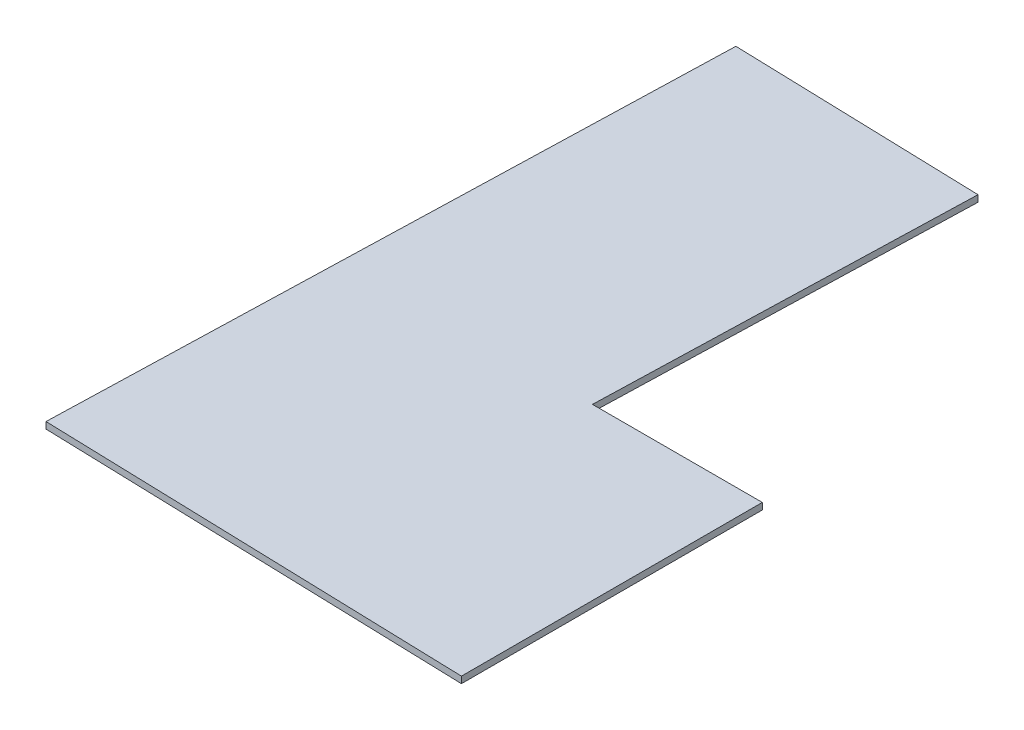
SolidWorks part; units mm, degrees
ref_plane "Front Plane" through (0, 0, 0) normal (0, 0, 1) x (1, 0, 0)
ref_plane "Top Plane" through (0, 0, 0) normal (0, 1, 0) x (1, 0, 0)
ref_plane "Right Plane" through (0, 0, 0) normal (1, 0, 0) x (0, 0, -1)
sketch "Sketch1" plane through (0, 0, 0) normal (0, 1, 0) x (1, 0, 0)
  line L1 (-241.1129, -200.9269) -> (-159.0136, -200.9269)
  line L6 (-159.0136, -200.9269) -> (-159.0136, -346.3773)
  line L7 (-159.0136, -346.3773) -> (-366.0236, -340.2039)
  line L8 (-366.0236, -340.2039) -> (-356.366, -16.3539)
  line L9 (-356.366, -16.3539) -> (-235.716, -19.9519)
  line L10 (-235.716, -19.9519) -> (-241.1129, -200.9269)
  dimension "D1" = 120.65
  dimension "D2" = 323.85
  dimension "D3" = 207.01
  dimension "D4" = 180.975
extrude "Boss-Extrude1" add sketch "Sketch1" along normal blind 3.175
